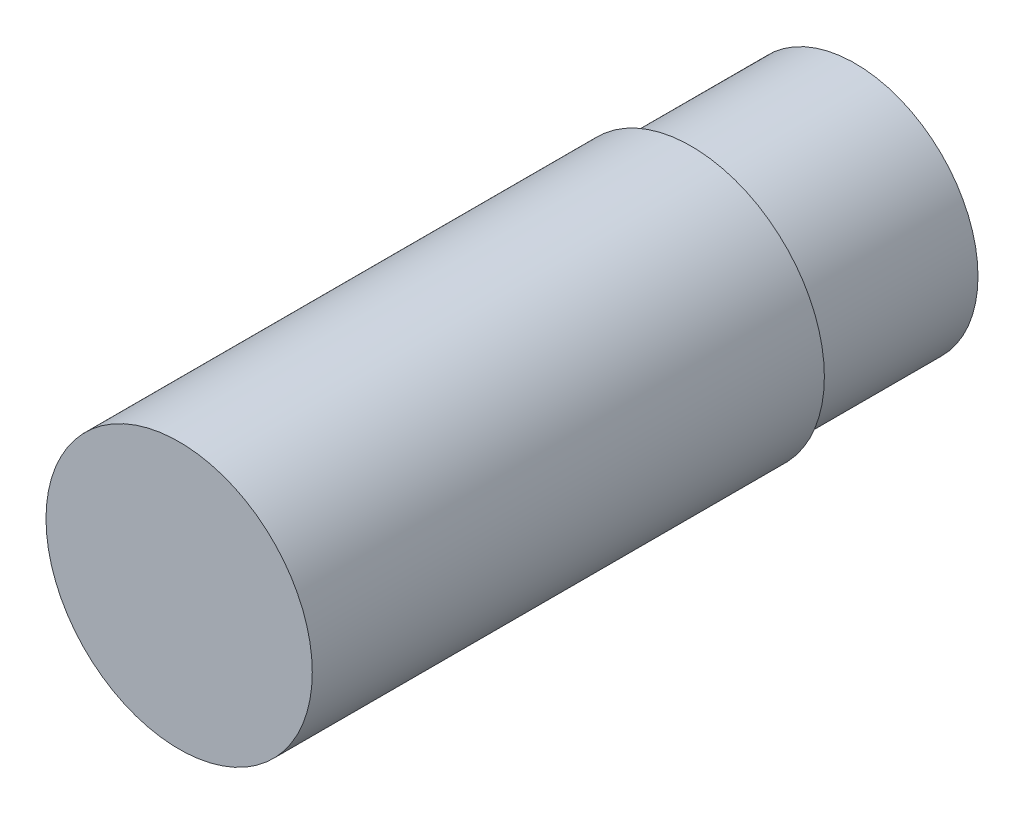
SolidWorks part; units mm, degrees
ref_plane "Front Plane" through (0, 0, 0) normal (0, 0, 1) x (1, 0, 0)
ref_plane "Top Plane" through (0, 0, 0) normal (0, 1, 0) x (1, 0, 0)
ref_plane "Right Plane" through (0, 0, 0) normal (1, 0, 0) x (0, 0, -1)
sketch "Sketch1" plane through (0, 0, 0) normal (0, 0, 1) x (1, 0, 0)
  circle A0 centre (0, 0) radius 1.524
  dimension "D1" = 3.048
extrude "Boss-Extrude1" add sketch "Sketch1" along normal blind 2.032
sketch "Sketch2" plane through (0, 0, 2.032) normal (0, 0, 1) x (1, 0, 0)
  circle A0 centre (0, 0) radius 1.651
  dimension "D1" = 3.302
extrude "Boss-Extrude2" add sketch "Sketch2" along normal blind 6.35 contours A0
